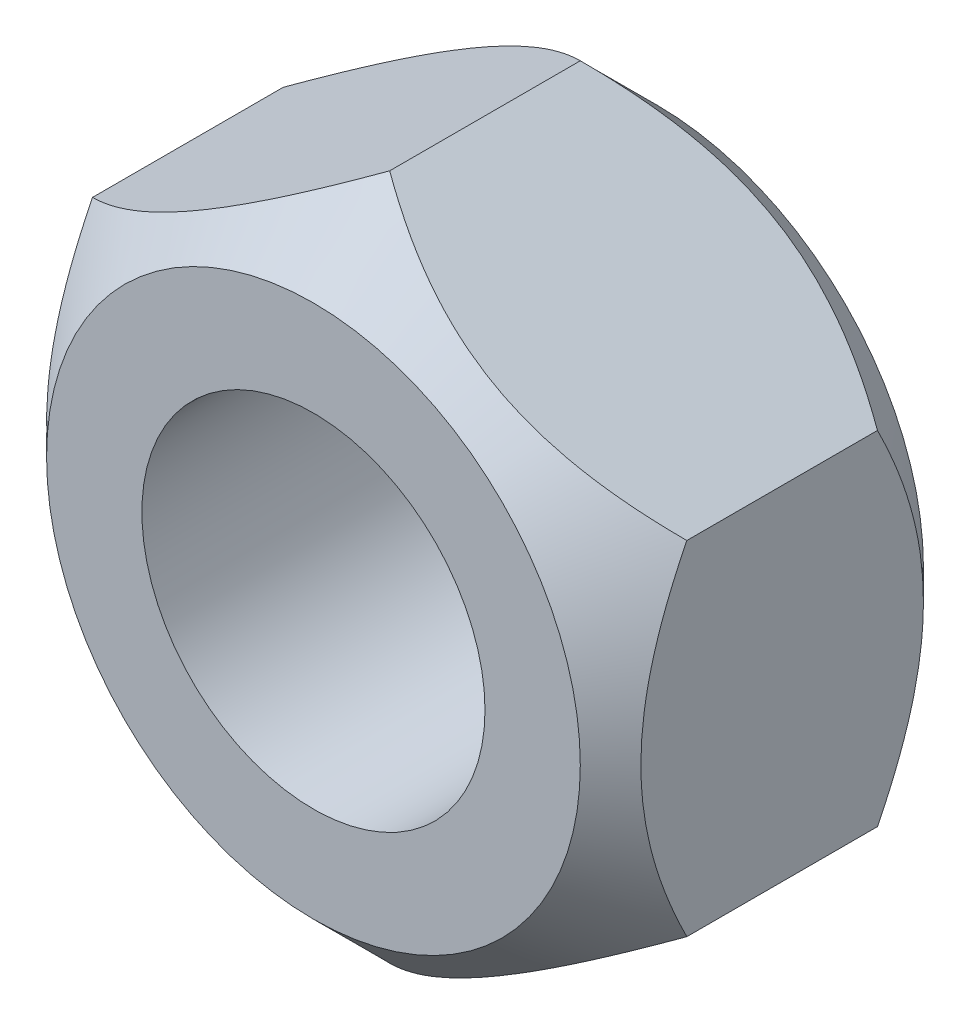
SolidWorks part; units mm, degrees
ref_plane "Front Plane" through (0, 0, 0) normal (0, 0, 1) x (1, 0, 0)
ref_plane "Top Plane" through (0, 0, 0) normal (0, 1, 0) x (1, 0, 0)
ref_plane "Right Plane" through (0, 0, 0) normal (1, 0, 0) x (0, 0, -1)
sketch "Sketch1" plane through (0, 0, 0) normal (0, 0, 1) x (1, 0, 0)
  line L1 (7.7942, -4.5) -> (7.7942, 4.5)
  line L2 (7.7942, 4.5) -> (0, 9)
  line L3 (0, 9) -> (-7.7942, 4.5)
  line L4 (-7.7942, 4.5) -> (-7.7942, -4.5)
  line L5 (-7.7942, -4.5) -> (0, -9)
  line L6 (0, -9) -> (7.7942, -4.5)
  circle A0 centre (0, 0) radius 7.7942 construction
  circle A1 centre (0, 0) radius 4.5
  dimension "D1" = 4.5
  dimension "D2" = 9
extrude "Boss-Extrude1" add sketch "Sketch1" along normal mid plane 9
sketch "Sketch2" plane through (0, 0, 4.5) normal (0, 0, 1) x (1, 0, 0)
  circle A0 centre (0, 0) radius 7
  point P3 (-22.2706, 0.6226)
  dimension "D1" = 7
extrude "Cut-Extrude1" cut sketch "Sketch2" against normal blind 9 draft 45 flip side to cut
mirror "Mirror1" about plane through (0, 0, 0) normal (0, 0, 1) of "Cut-Extrude1"
